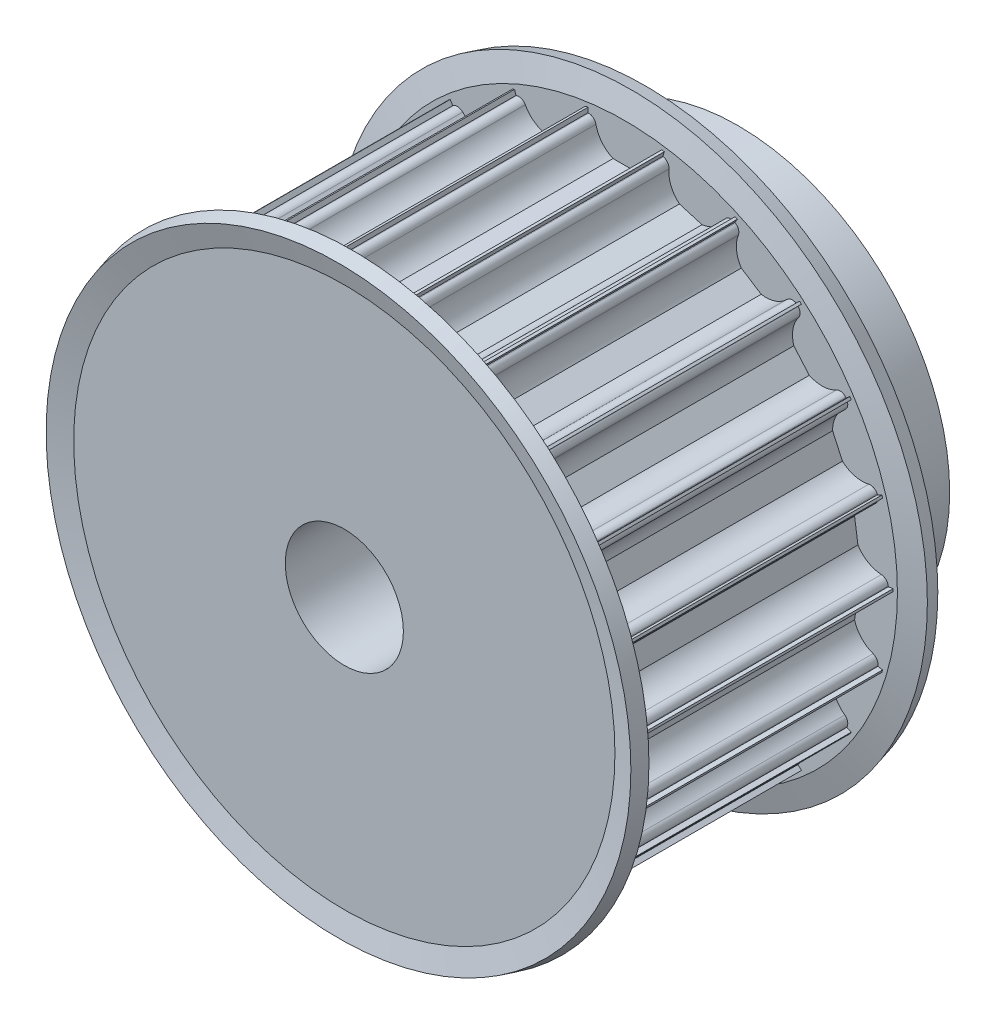
SolidWorks part; units mm, degrees
ref_plane "Plan de face" through (0, 0, 0) normal (0, 0, 1) x (1, 0, 0)
ref_plane "Plan de dessus" through (0, 0, 0) normal (0, 1, 0) x (1, 0, 0)
ref_plane "Plan de droite" through (0, 0, 0) normal (1, 0, 0) x (0, 0, -1)
ref_axis "Axe1" through (0, 0, 55) along (0, 0, -1)
sketch "Esquisse1" plane through (0, 0, 0) normal (1, 0, 0) x (0, 0, -1)
  line L0 (0, 6) -> (0, 27.25)
  line L1 (0, 27.25) -> (30, 27.25)
  line L2 (30, 27.25) -> (30, 21.5)
  line L3 (30, 21.5) -> (40, 21.5)
  line L4 (40, 21.5) -> (40, 6)
  line L5 (40, 6) -> (0, 6)
  line L6 (-55, 0) -> (55, 0) construction
  dimension "D1" = 30
  dimension "D2" = 10
  dimension "D3" = 15.5
  dimension "D4" = 21.25
  dimension "D5" = 6
revolve "Révolution1" add sketch "Esquisse1" angle 360 about axis through (0, 0, 55) along (0, 0, -1)
sketch "Esquisse2" plane through (0, 0, 0) normal (0, 0, 1) x (1, 0, 0)
  line L0 (3.6742, 26.5) -> (3.75, 26.5)
  line L1 (-3.75, 28.5) -> (3.75, 28.5)
  line L2 (-3.75, 28.5) -> (-3.75, 26.5)
  line L3 (-3.75, 26.5) -> (-3.6742, 26.5)
  line L4 (3.75, 28.5) -> (3.75, 26.5)
  line L5 (-1.199, 23.75) -> (1.199, 23.75)
  arc A0 (-2.9394, 25.9) -> (-1.199, 23.75) centre (0, 26.5) ccw
  arc A1 (-2.9394, 25.9) -> (-3.6742, 26.5) centre (-3.6742, 25.75) ccw
  arc A2 (2.9394, 25.9) -> (3.6742, 26.5) centre (3.6742, 25.75) cw
  arc A3 (1.199, 23.75) -> (2.9394, 25.9) centre (0, 26.5) ccw
  dimension "D3" = 3
  dimension "D5" = 0.75
  dimension "D6" = 0.75
  dimension "D1" = 7.5
  dimension "D2" = 2
  dimension "D4" = 26.5
  dimension "D7" = 2.75
extrude "Enlèv. mat.-Extru.1" cut sketch "Esquisse2" against normal through all
pattern_circular "Répétition circulaire1" count 22 over 360 about axis through (0, 0, 0) along (0, 0, 1) of "Enlèv. mat.-Extru.1"
sketch "Esquisse3" plane through (0, 0, 0) normal (1, 0, 0) x (0, 0, -1)
  line L0 (0, 25.679) -> (0, 23.1257) construction
  line L1 (0, 25.679) -> (0, 24.8409)
  line L4 (0, 22.6907) -> (1.5, 22.6907)
  line L5 (0, 22.6907) -> (0, 27.6907)
  line L6 (0, 27.6907) -> (1.5, 27.6907) construction
  line L7 (1.5, 22.6907) -> (1.5, 27.6907)
  line L11 (1.5, 27.6907) -> (0.0511, 27.3025) construction
  line L12 (1.5, 27.6907) -> (0.8569, 30.0907)
  line L13 (0.0511, 27.3025) -> (-0.592, 29.7025)
  line L14 (0.8569, 30.0907) -> (-0.592, 29.7025)
  line L16 (30, 26.9907) -> (0, 26.9907) construction
  line L17 (15, 26.9539) -> (15, -31.6769) construction
  line L18 (0, 26.9539) -> (30, 26.9539) construction
  line L19 (28.5, 27.6907) -> (29.9489, 27.3025) construction
  line L20 (30, 27.6907) -> (28.5, 27.6907) construction
  line L21 (29.1431, 30.0907) -> (30.592, 29.7025)
  line L22 (29.9489, 27.3025) -> (30.592, 29.7025)
  line L23 (28.5, 27.6907) -> (29.1431, 30.0907)
  line L24 (28.5, 22.6907) -> (28.5, 27.6907)
  line L25 (30, 22.6907) -> (30, 27.6907)
  line L26 (30, 22.6907) -> (28.5, 22.6907)
  line L27 (30, 25.679) -> (30, 24.8409)
  dimension "D1" = 1.5
  dimension "D2" = 5
  dimension "D3" = 165
  dimension "D4" = 1.5
  dimension "D5" = 2.4
  dimension "D6" = 90
  dimension "D7" = 90
  dimension "D8" = 0.7
revolve "Révolution3" add sketch "Esquisse3" angle 360 about axis through (0, 0, 55) along (0, 0, -1)
